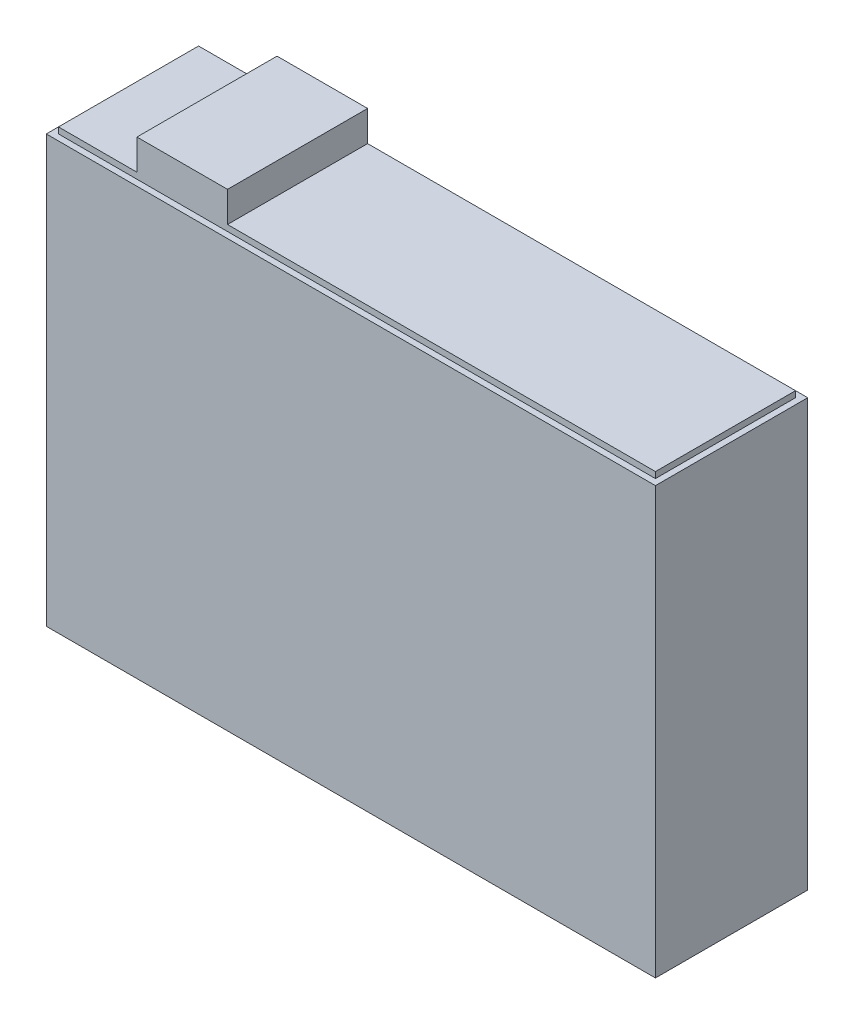
SolidWorks part; units mm, degrees
ref_plane "Front Plane" through (0, 0, 0) normal (0, 0, 1) x (1, 0, 0)
ref_plane "Top Plane" through (0, 0, 0) normal (0, 1, 0) x (1, 0, 0)
ref_plane "Right Plane" through (0, 0, 0) normal (1, 0, 0) x (0, 0, -1)
sketch "Sketch1" plane through (0, 0, 0) normal (0, 1, 0) x (1, 0, 0)
  line L0 (0, 1.25) -> (0, -1.25) construction
  line L1 (-5, 1.25) -> (5, 1.25)
  line L2 (-5, 1.25) -> (-5, -1.25)
  line L3 (-5, -1.25) -> (5, -1.25)
  line L4 (5, 1.25) -> (5, -1.25)
  dimension "D1" = 10
  dimension "D2" = 2.5
extrude "Boss-Extrude1" add sketch "Sketch1" along normal blind 7
sketch "Sketch2" plane through (0, 7, 0) normal (0, 1, 0) x (1, 0, 0)
  line L12 (-4.9, 1.15) -> (-4.9, -1.15)
  line L13 (-4.9, -1.15) -> (4.9, -1.15)
  line L14 (4.9, -1.15) -> (4.9, 1.15)
  line L15 (4.9, 1.15) -> (-4.9, 1.15)
  line L16 (-4.9, 1.15) -> (-4.9, -1.15)
  line L17 (-4.9, -1.15) -> (4.9, -1.15)
  line L18 (4.9, -1.15) -> (4.9, 1.15)
  line L19 (4.9, 1.15) -> (-4.9, 1.15)
  dimension "D1" = 0.1
extrude "Boss-Extrude2" add sketch "Sketch2" along normal blind 0.1
sketch "Sketch3" plane through (0, 7.1, 0) normal (0, 1, 0) x (1, 0, 0)
  line L0 (4.9, 1.15) -> (-4.9, 1.15) construction
  line L1 (-3.6119, 1.15) -> (-2.1248, 1.15)
  line L2 (-3.6119, 1.15) -> (-3.6119, -1.15)
  line L3 (-3.6119, -1.15) -> (-2.1248, -1.15)
  line L4 (-2.1248, 1.15) -> (-2.1248, -1.15)
  line L5 (-4.9, -1.15) -> (4.9, -1.15) construction
extrude "Boss-Extrude3" add sketch "Sketch3" along normal blind 0.5
